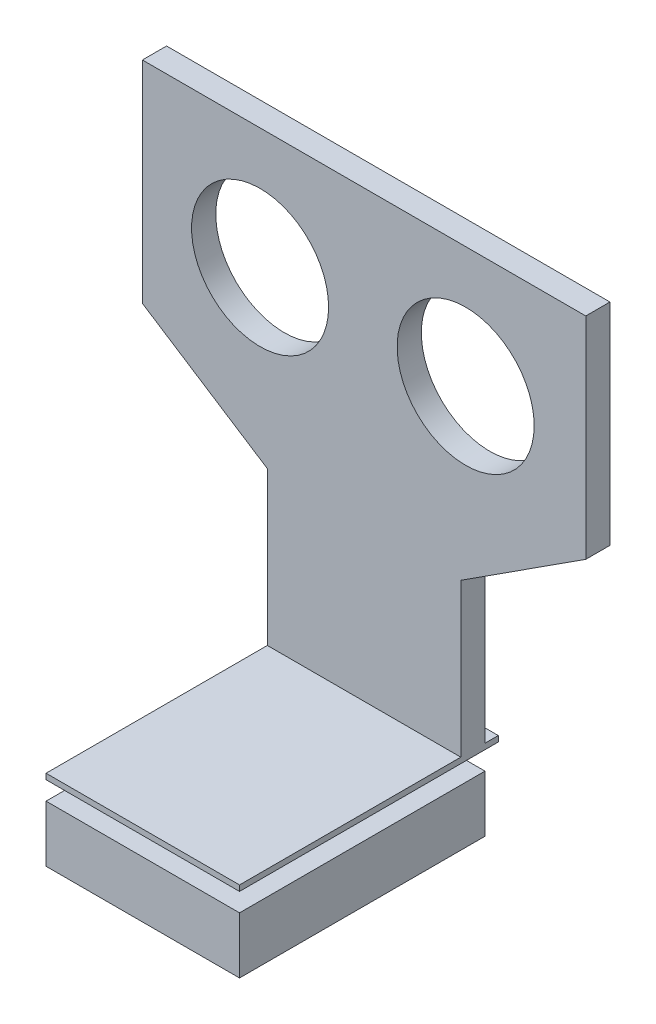
SolidWorks part; units mm, degrees
ref_plane "Plano frontal" through (0, 0, 0) normal (0, 0, 1) x (1, 0, 0)
ref_plane "Plano superior" through (0, 0, 0) normal (0, 1, 0) x (1, 0, 0)
ref_plane "Plano direito" through (0, 0, 0) normal (1, 0, 0) x (0, 0, -1)
sketch "Esboço1" plane through (0, 0, 0) normal (0, 0, 1) x (1, 0, 0)
  line L2 (0, 0) -> (0, 26.15)
  line L4 (55, 0) -> (55, 26.15)
  line L14 (15.5, -10) -> (0, 0)
  line L20 (15.5, -10) -> (15.5, -32)
  line L33 (15.5, -32) -> (39.5, -32)
  line L34 (39.5, -10) -> (39.5, -32)
  line L39 (39.5, -10) -> (55, 0)
  line L40 (-8.9796, 11.15) -> (5, 11.15) construction
  line L49 (0, 26.15) -> (55, 26.15)
  line L54 (21.8782, 11.15) -> (33.7849, 11.15) construction
  line L55 (50, 11.15) -> (4.7, 11.15) construction
  line L56 (27.35, 21.4) -> (27.35, 0.9) construction
  line L57 (4.6, 21.4) -> (50.1, 21.4) construction
  line L58 (50.1, 0.9) -> (4.6, 0.9) construction
  line L59 (40.1, 19.65) -> (40.1, 2.65) construction
  arc A6 (40.1, 2.65) -> (40.1, 19.65) centre (40.1, 11.15) ccw construction
  circle A9 centre (40.1, 11.15) radius 8.5
  circle A10 centre (14.6, 11.15) radius 8.5
  point P1 (0, 0)
  dimension "D2" = 15
  dimension "D4" = 22
  dimension "D7" = 24
  dimension "D8" = 10
  dimension "D11" = 15.5
  dimension "D12" = 55
extrude "Ressalto-extrusão2" add sketch "Esboço1" along normal blind 3
sketch "Esboço2" plane through (0, 0, 3) normal (0, 0, 1) x (1, 0, 0)
  line L0 (39.5, -32) -> (39.5, -10) construction
  line L1 (15.5, -32) -> (39.5, -32)
  line L2 (15.5, -32) -> (15.5, -29)
  line L3 (15.5, -29) -> (39.5, -29)
  line L4 (39.5, -32) -> (39.5, -29)
  dimension "D1" = 3
extrude "Ressalto-extrusão4" add sketch "Esboço2" along normal up to surface (27.45 mm away) and the other way up to surface (4.65 mm away) contours L2 L1 L4 L3
sketch "Sketch2" plane through (0, -32, 0) normal (0, -1, 0) x (1, 0, 0)
  line L1 (15.5, 30.45) -> (39.5, 30.45)
  line L2 (15.5, 30.45) -> (15.5, 0)
  line L3 (15.5, 0) -> (39.5, 0)
  line L4 (39.5, 30.45) -> (39.5, 0)
  circle A0 centre (27.1057, 19.6) radius 2.9
  dimension "D1" = 5.8
extrude "Boss-Extrude2" add sketch "Sketch2" along normal blind 1
sketch "Sketch3" plane through (0, -32, 0) normal (0, -1, 0) x (1, 0, 0)
  circle A1 centre (27.1057, 19.6) radius 34.5173
  circle A2 centre (27.1057, 19.6) radius 2.9
  dimension "D1" = 5.8
extrude "Cut-Extrude1" cut sketch "Sketch3" against normal blind 2.3
sketch "Sketch4" plane through (0, -33, 0) normal (0, -1, 0) x (1, 0, 0)
  line L1 (15.5, 30.45) -> (39.5, 30.45)
  line L2 (15.5, 30.45) -> (15.5, 0)
  line L3 (15.5, 0) -> (39.5, 0)
  line L4 (39.5, 30.45) -> (39.5, 0)
  arc A0 (29.5905, 13.5937) -> (24.4693, 13.6587) centre (27.1057, 19.6) ccw
  arc A2 (24.4693, 13.6587) -> (29.5905, 13.5937) centre (27.0255, 13.2749) ccw
  dimension "D1" = 13
extrude "Boss-Extrude3" add sketch "Sketch4" along normal up to surface (6 mm away)
